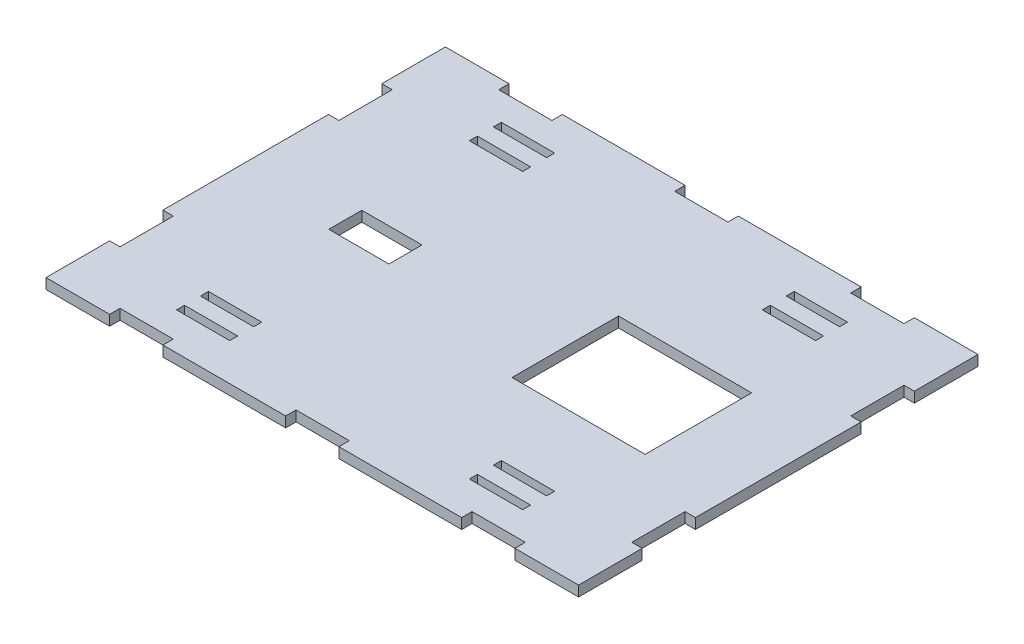
SolidWorks part; units mm, degrees
material "Very Low Density PE (SS)"
ref_plane "Front Plane" through (0, 0, 0) normal (0, 0, 1) x (1, 0, 0)
ref_plane "Top Plane" through (0, 0, 0) normal (0, 1, 0) x (1, 0, 0)
ref_plane "Right Plane" through (0, 0, 0) normal (1, 0, 0) x (0, 0, -1)
sketch "Sketch1" plane through (0, 0, 0) normal (0, 1, 0) x (1, 0, 0)
  line L0 (-125, 0) -> (125, 0) construction
  line L1 (-100, 75) -> (-76.1, 75)
  line L2 (-100, 75) -> (-100, 51.1)
  line L3 (-100, -75) -> (-76.1, -75)
  line L4 (100, 75) -> (100, 51.1)
  line L5 (0, 75) -> (0, -75) construction
  line L6 (-100, -55) -> (100, -55) construction
  line L11 (-65, -49) -> (-45, -49)
  line L12 (-65, -58) -> (-45, -58)
  line L25 (-65, -58) -> (-65, -61)
  line L31 (20, 20) -> (70, 20)
  line L32 (-65, -61) -> (-45, -61)
  line L33 (-45, -58) -> (-45, -61)
  line L34 (-45, -52) -> (-45, -49)
  line L35 (-65, -52) -> (-45, -52)
  line L36 (-65, -52) -> (-65, -49)
  line L37 (65, -61) -> (45, -61)
  line L38 (45, -58) -> (45, -61)
  line L39 (65, -58) -> (45, -58)
  line L40 (65, -58) -> (65, -61)
  line L41 (65, -52) -> (65, -49)
  line L42 (65, -52) -> (45, -52)
  line L43 (45, -52) -> (45, -49)
  line L44 (65, -49) -> (45, -49)
  line L45 (65, 52) -> (45, 52)
  line L46 (45, 52) -> (45, 49)
  line L47 (65, 49) -> (45, 49)
  line L48 (65, 52) -> (65, 49)
  line L49 (65, 58) -> (65, 61)
  line L50 (65, 58) -> (45, 58)
  line L51 (45, 58) -> (45, 61)
  line L52 (65, 61) -> (45, 61)
  line L53 (-65, 61) -> (-45, 61)
  line L54 (-45, 58) -> (-45, 61)
  line L55 (-65, 58) -> (-45, 58)
  line L56 (-65, 58) -> (-65, 61)
  line L57 (-65, 52) -> (-65, 49)
  line L58 (-65, 52) -> (-45, 52)
  line L59 (-45, 52) -> (-45, 49)
  line L60 (-65, 49) -> (-45, 49)
  line L61 (76.1, -71.1) -> (56.1, -71.1)
  line L63 (-76.1, -75) -> (-76.1, -71.1)
  line L64 (-76.1, -71.1) -> (-56.1, -71.1)
  line L65 (-56.1, -75) -> (-56.1, -71.1)
  line L66 (56.1, -75) -> (56.1, -71.1)
  line L68 (76.1, -75) -> (76.1, -71.1)
  line L69 (10, -75) -> (56.1, -75)
  line L70 (-10, -71.1) -> (10, -71.1)
  line L71 (-10, -71.1) -> (-10, -75)
  line L73 (10, -71.1) -> (10, -75)
  line L74 (-10, -71.1) -> (10, -75) construction
  line L75 (-10, -75) -> (10, -71.1) construction
  line L76 (-56.1, -75) -> (-10, -75)
  line L77 (76.1, -75) -> (100, -75)
  line L78 (76.1, 75) -> (76.1, 71.1)
  line L79 (56.1, 75) -> (56.1, 71.1)
  line L80 (76.1, 71.1) -> (56.1, 71.1)
  line L81 (10, 71.1) -> (10, 75)
  line L82 (-10, 71.1) -> (10, 71.1)
  line L83 (-10, 71.1) -> (-10, 75)
  line L84 (-56.1, 75) -> (-56.1, 71.1)
  line L85 (-76.1, 71.1) -> (-56.1, 71.1)
  line L86 (-76.1, 75) -> (-76.1, 71.1)
  line L87 (-10, 75) -> (0, 75) construction
  line L88 (10, 75) -> (56.1, 75)
  line L89 (0, 75) -> (10, 75) construction
  line L90 (-76.1, 75) -> (-56.1, 75) construction
  line L91 (-56.1, 75) -> (-10, 75)
  line L92 (56.1, 75) -> (76.1, 75) construction
  line L93 (76.1, 75) -> (100, 75)
  line L94 (100, -31.1) -> (96.1, -31.1)
  line L95 (100, 51.1) -> (96.1, 51.1)
  line L96 (100, 51.1) -> (100, 31.1) construction
  line L97 (100, 31.1) -> (96.1, 31.1)
  line L98 (96.1, 51.1) -> (96.1, 31.1)
  line L99 (96.1, -51.1) -> (96.1, -31.1)
  line L100 (100, -51.1) -> (96.1, -51.1)
  line L101 (100, -51.1) -> (100, -31.1) construction
  line L102 (100, 51.1) -> (100, 31.1) construction
  line L103 (100, 31.1) -> (100, -31.1)
  line L104 (100, -31.1) -> (100, -51.1) construction
  line L105 (100, -51.1) -> (100, -75)
  line L106 (-100, -31.1) -> (-96.1, -31.1)
  line L107 (-96.1, -51.1) -> (-96.1, -31.1)
  line L108 (-100, -51.1) -> (-96.1, -51.1)
  line L109 (-100, 31.1) -> (-96.1, 31.1)
  line L110 (-100, 51.1) -> (-96.1, 51.1)
  line L111 (-96.1, 51.1) -> (-96.1, 31.1)
  line L112 (-100, 51.1) -> (-100, 31.1) construction
  line L113 (-100, 31.1) -> (-100, -31.1)
  line L114 (-100, -31.1) -> (-100, -51.1) construction
  line L115 (-100, -51.1) -> (-100, -75)
  line L117 (-62.6, 6.2) -> (-40, 6.2)
  line L118 (-62.6, 6.2) -> (-62.6, -6.2)
  line L119 (-62.6, -6.2) -> (-40, -6.2)
  line L120 (-40, 6.2) -> (-40, -6.2)
  line L121 (-62.6, 6.2) -> (-40, -6.2) construction
  line L122 (-62.6, -6.2) -> (-40, 6.2) construction
  line L123 (20, 20) -> (20, -20)
  line L124 (20, -20) -> (70, -20)
  line L125 (70, 20) -> (70, -20)
  line L126 (20, 20) -> (70, -20) construction
  line L127 (20, -20) -> (70, 20) construction
  point P0 (0, 0)
  point P29 (0, 0)
  point P30 (45, 0)
  point P57 (0, -73.05)
  point P82 (-51.3, 0)
  dimension "D2" = 150
  dimension "D3" = 3
  dimension "D4" = 20
  dimension "D5" = 23.9
  dimension "D6" = 20
  dimension "D7" = 40
  dimension "D8" = 40
  dimension "D9" = 3
  dimension "D10" = 45
  dimension "D11" = 20
  dimension "D12" = 3.9
  dimension "D13" = 20
  dimension "D14" = 12.4
  dimension "D15" = 23.9
  dimension "D16" = 20
  dimension "D17" = 3.9
  dimension "D18" = 200
  dimension "D19" = 22.6
  dimension "D20" = 50
  dimension "D21" = 30
extrude "Boss-Extrude1" add sketch "Sketch1" along normal blind 3.9
